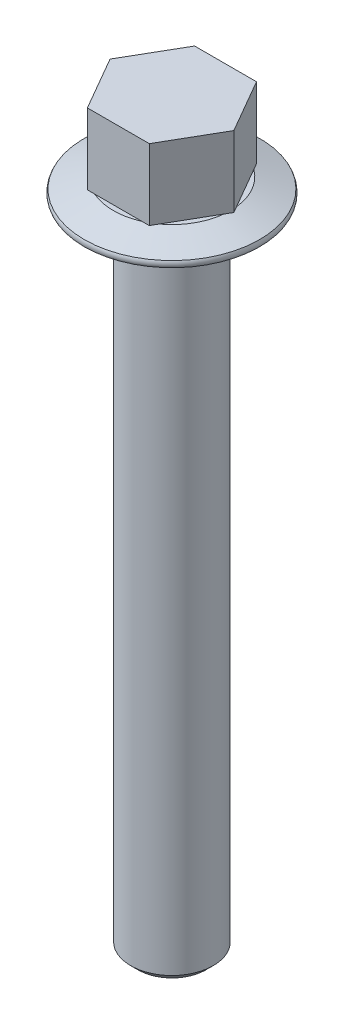
SolidWorks part; units mm, degrees
ref_plane "Front Plane" through (0, 0, 0) normal (0, 0, 1) x (1, 0, 0)
ref_plane "Top Plane" through (0, 0, 0) normal (0, 1, 0) x (1, 0, 0)
ref_plane "Right Plane" through (0, 0, 0) normal (1, 0, 0) x (0, 0, -1)
sketch "Sketch1" plane through (0, 0, 0) normal (0, 0, 1) x (1, 0, 0)
  line L0 (0, 0) -> (8.5, 0)
  line L2 (8.5, 0.6) -> (5.6809, 1.6261)
  line L3 (5.6809, 1.6261) -> (0, 1.6261)
  line L4 (0, 1.6261) -> (0, 0)
  arc A0 (8.5, 0.6) -> (8.5, 0) centre (7.9804, 0.3) cw
  dimension "D5" = 0.6
  dimension "D1" = 0.6
  dimension "D2" = 20
  dimension "D3" = 3
  dimension "D4" = 8.5
revolve "Revolve1" add sketch "Sketch1" angle 360 about L4
sketch "Sketch2" plane through (0, 1.6261, 0) normal (0, 1, 0) x (1, 0, 0)
  line L1 (6, 0) -> (3, 5.1962)
  line L2 (3, 5.1962) -> (-3, 5.1962)
  line L3 (-3, 5.1962) -> (-6, 0)
  line L4 (-6, 0) -> (-3, -5.1962)
  line L5 (-3, -5.1962) -> (3, -5.1962)
  line L6 (3, -5.1962) -> (6, 0)
  circle A0 centre (0, 0) radius 5.1962 construction
  dimension "D1" = 12
extrude "Boss-Extrude1" add sketch "Sketch2" along normal blind 6.88
sketch "Sketch3" plane through (0, 0, 0) normal (0, -1, 0) x (1, 0, 0)
  circle A0 centre (0, 0) radius 4
extrude "Boss-Extrude2" add sketch "Sketch3" along normal blind 64
sketch "Sketch4" plane through (0, -64, 0) normal (0, -1, 0) x (1, 0, 0)
  circle A1 centre (0, 0) radius 4
  circle A2 centre (0, 0) radius 4
  dimension "D1" = 0
extrude "Cut-Extrude1" cut sketch "Sketch4" against normal blind 0.7 draft 45 draft outward yes
chamfer "Chamfer1" distance 0.7 angle 45 1 edges at (0, -63.3, -4)
